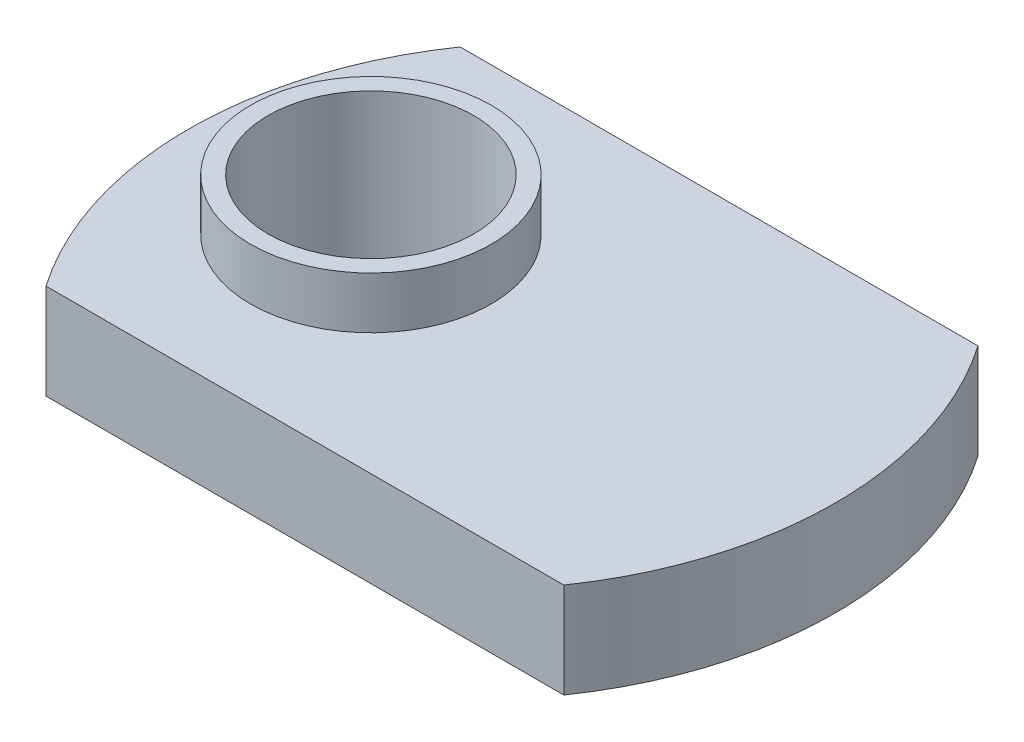
SolidWorks part; units mm, degrees
ref_plane "Front Plane" through (0, 0, 0) normal (0, 0, 1) x (1, 0, 0)
ref_plane "Top Plane" through (0, 0, 0) normal (0, 1, 0) x (1, 0, 0)
ref_plane "Right Plane" through (0, 0, 0) normal (1, 0, 0) x (0, 0, -1)
sketch "Sketch2" plane through (0, 0, 0) normal (0, 1, 0) x (1, 0, 0)
  line L1 (0, 0) -> (20, 0)
  line L2 (0, 0) -> (0, 16) construction
  line L3 (0, 16) -> (20, 16)
  line L4 (20, 0) -> (20, 16) construction
  line L5 (0, 0) -> (20, 16) construction
  line L6 (0, 16) -> (20, 0) construction
  arc A0 (20, 16) -> (20, 0) centre (8.45, 8) cw
  arc A1 (0, 0) -> (0, 16) centre (11.55, 8) cw
  circle A2 centre (4.55, 8) radius 3.9688
  point P4 (10, 8)
  point P8 (-2.5, 8)
  point P9 (22.5, 8)
  dimension "D4" = 7.9375
  dimension "D1" = 20
  dimension "D2" = 16
  dimension "D3" = 25
  dimension "D5" = 7
extrude "Boss-Extrude1" add sketch "Sketch2" along normal blind 3.68
sketch "Sketch3" plane through (0, 3.68, 0) normal (0, 1, 0) x (1, 0, 0)
  circle A0 centre (4.55, 8) radius 3.9688 construction
  circle A1 centre (4.55, 8) radius 3.9688
  circle A2 centre (4.55, 8) radius 4.65
  dimension "D1" = 9.3
extrude "Boss-Extrude2" add sketch "Sketch3" along normal blind 2
